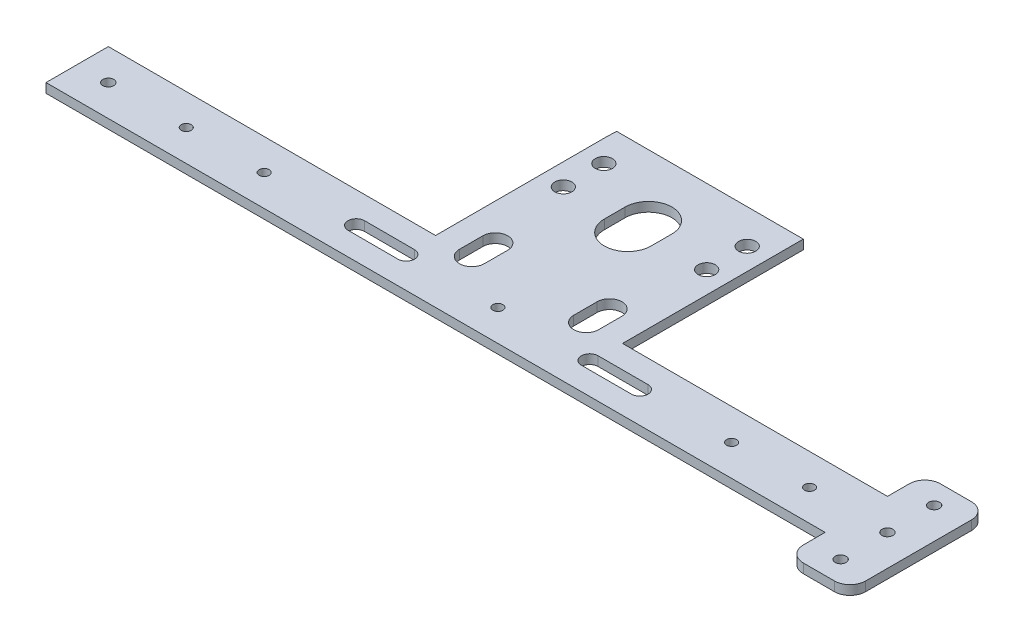
SolidWorks part; units mm, degrees
material "A-玻璃纤维"
ref_plane "前视基准面" through (0, 0, 0) normal (0, 0, 1) x (1, 0, 0)
ref_plane "上视基准面" through (0, 0, 0) normal (0, 1, 0) x (1, 0, 0)
ref_plane "右视基准面" through (0, 0, 0) normal (1, 0, 0) x (0, 0, -1)
sketch "草图1" plane through (0, 0, 0) normal (0, 1, 0) x (1, 0, 0)
  line L1 (-135, 50) -> (135, 50)
  line L2 (-135, 50) -> (-135, -50)
  line L3 (-135, -50) -> (135, -50)
  line L4 (135, 50) -> (135, -50)
  line L5 (-135, 50) -> (135, -50) construction
  line L6 (-135, -50) -> (135, 50) construction
  point P0 (0, 0)
  dimension "D1" = 270
  dimension "D2" = 100
extrude "凸台-拉伸1" add sketch "草图1" along normal blind 3
sketch "草图2" plane through (0, 3, 0) normal (0, 1, 0) x (1, 0, 0)
  line L0 (0, 50) -> (0, -50) construction
  line L1 (135, 50) -> (-135, 50) construction
  line L2 (-135, -50) -> (135, -50) construction
  line L3 (-135, 0) -> (135, 0) construction
  line L4 (-135, 50) -> (-135, -50) construction
  line L5 (135, -50) -> (135, 50) construction
  line L6 (141.2853, -40) -> (-157.6953, -40) construction
  circle A2 centre (-125, 40) radius 1.6
  circle A3 centre (-125, 0) radius 1.6
  circle A4 centre (125, 0) radius 1.6
  circle A5 centre (125, 40) radius 1.6
  circle A6 centre (-125, -40) radius 1.75
  circle A7 centre (-100, -40) radius 1.6
  circle A8 centre (-75, -40) radius 1.6
  circle A9 centre (0, -40) radius 1.6
  circle A10 centre (75, -40) radius 1.6
  circle A11 centre (100, -40) radius 1.6
  circle A12 centre (125, -40) radius 1.75
  dimension "D1" = 3.2
  dimension "D2" = 3.5
  dimension "D3" = 3.2
  dimension "D5" = 10
  dimension "D7" = 25
  dimension "D8" = 50
  dimension "D9" = 40
  dimension "D10" = 40
  dimension "D6" = 10
extrude "切除-拉伸1" cut sketch "草图2" against normal blind 3
sketch "草图4" plane through (0, 3, 0) normal (0, 1, 0) x (1, 0, 0)
  line L0 (0, -106.0486) -> (0, 112.9076) construction
  line L1 (110, -50) -> (110, 50) construction
  line L2 (-135, -50) -> (135, -50) construction
  line L3 (135, 50) -> (-135, 50) construction
  line L4 (91.6667, -50) -> (91.6667, 65) construction
  line L5 (110, -30) -> (110, -23.3333) construction
  line L6 (102.5, -30) -> (102.5, -23.3333)
  line L7 (117.5, -30) -> (117.5, -23.3333)
  line L8 (110, 1.6667) -> (110, 8.3333) construction
  line L9 (102.5, 1.6667) -> (102.5, 8.3333)
  line L10 (117.5, 1.6667) -> (117.5, 8.3333)
  line L11 (110, 28.3333) -> (110, 35) construction
  line L12 (102.5, 28.3333) -> (102.5, 35)
  line L13 (117.5, 28.3333) -> (117.5, 35)
  line L14 (135, -30) -> (-135, -30) construction
  line L15 (135, -50) -> (135, 50) construction
  line L16 (-135, 50) -> (-135, -50) construction
  line L17 (91.6667, -30) -> (91.6667, -22.5) construction
  line L18 (87.6667, -30) -> (87.6667, -22.5)
  line L19 (95.6667, -30) -> (95.6667, -22.5)
  line L20 (91.6667, -10.5) -> (91.6667, -6.5) construction
  line L21 (87.6667, -10.5) -> (87.6667, -6.5)
  line L22 (95.6667, -10.5) -> (95.6667, -6.5)
  line L23 (91.6667, 8.5) -> (91.6667, 12.5) construction
  line L24 (87.6667, 8.5) -> (87.6667, 12.5)
  line L25 (95.6667, 8.5) -> (95.6667, 12.5)
  line L26 (136.9036, 35) -> (-135, 35) construction
  line L27 (91.6667, 35) -> (91.6667, 27.5) construction
  line L28 (95.6667, 35) -> (95.6667, 27.5)
  line L29 (87.6667, 35) -> (87.6667, 27.5)
  line L30 (73.3333, -30) -> (73.3333, -23.3333) construction
  line L31 (65.8333, -30) -> (65.8333, -23.3333) construction
  line L32 (80.8333, -30) -> (80.8333, -23.3333) construction
  line L33 (73.3333, 1.6667) -> (73.3333, 8.3333) construction
  line L34 (65.8333, 1.6667) -> (65.8333, 8.3333)
  line L35 (80.8333, 1.6667) -> (80.8333, 8.3333)
  line L36 (73.3333, 28.3333) -> (73.3333, 35) construction
  line L37 (65.8333, 28.3333) -> (65.8333, 35)
  line L38 (80.8333, 28.3333) -> (80.8333, 35)
  line L39 (55, -30) -> (55, -22.5) construction
  line L40 (51, -30) -> (51, -22.5)
  line L41 (59, -30) -> (59, -22.5)
  line L42 (55, -10.5) -> (55, -6.5) construction
  line L43 (51, -10.5) -> (51, -6.5)
  line L44 (59, -10.5) -> (59, -6.5)
  line L45 (55, 8.5) -> (55, 12.5) construction
  line L46 (51, 8.5) -> (51, 12.5)
  line L47 (59, 8.5) -> (59, 12.5)
  line L48 (55, 35) -> (55, 27.5) construction
  line L49 (59, 35) -> (59, 27.5)
  line L50 (51, 35) -> (51, 27.5)
  line L51 (36.6667, -30) -> (36.6667, -23.3333) construction
  line L52 (29.1667, -30) -> (29.1667, -23.3333)
  line L53 (44.1667, -30) -> (44.1667, -23.3333)
  line L54 (36.6667, 1.6667) -> (36.6667, 8.3333) construction
  line L55 (29.1667, 1.6667) -> (29.1667, 8.3333)
  line L56 (44.1667, 1.6667) -> (44.1667, 8.3333)
  line L57 (36.6667, 28.3333) -> (36.6667, 35) construction
  line L58 (29.1667, 28.3333) -> (29.1667, 35)
  line L59 (44.1667, 28.3333) -> (44.1667, 35)
  line L60 (18.3333, -30) -> (18.3333, -22.5) construction
  line L61 (14.3333, -30) -> (14.3333, -22.5)
  line L62 (22.3333, -30) -> (22.3333, -22.5)
  line L63 (18.3333, -10.5) -> (18.3333, -6.5) construction
  line L64 (14.3333, -10.5) -> (14.3333, -6.5) construction
  line L65 (22.3333, -10.5) -> (22.3333, -6.5) construction
  line L66 (18.3333, 8.5) -> (18.3333, 12.5) construction
  line L67 (14.3333, 8.5) -> (14.3333, 12.5) construction
  line L68 (22.3333, 8.5) -> (22.3333, 12.5) construction
  line L69 (18.3333, 35) -> (18.3333, 27.5) construction
  line L70 (22.3333, 35) -> (22.3333, 27.5)
  line L71 (14.3333, 35) -> (14.3333, 27.5)
  line L72 (0, -30) -> (0, -23.3333) construction
  line L73 (-7.5, -30) -> (-7.5, -23.3333) construction
  line L74 (7.5, -30) -> (7.5, -23.3333) construction
  line L75 (0, 1.6667) -> (0, 8.3333) construction
  line L76 (-7.5, 1.6667) -> (-7.5, 8.3333)
  line L77 (7.5, 1.6667) -> (7.5, 8.3333)
  line L78 (0, 28.3333) -> (0, 35) construction
  line L79 (-7.5, 28.3333) -> (-7.5, 35)
  line L80 (7.5, 28.3333) -> (7.5, 35)
  line L81 (-18.3333, -30) -> (-18.3333, -22.5) construction
  line L82 (-22.3333, -30) -> (-22.3333, -22.5)
  line L83 (-14.3333, -30) -> (-14.3333, -22.5)
  line L84 (-18.3333, -10.5) -> (-18.3333, -6.5) construction
  line L85 (-22.3333, -10.5) -> (-22.3333, -6.5) construction
  line L86 (-14.3333, -10.5) -> (-14.3333, -6.5) construction
  line L87 (-18.3333, 8.5) -> (-18.3333, 12.5) construction
  line L88 (-22.3333, 8.5) -> (-22.3333, 12.5) construction
  line L89 (-14.3333, 8.5) -> (-14.3333, 12.5) construction
  line L90 (-18.3333, 35) -> (-18.3333, 27.5) construction
  line L91 (-14.3333, 35) -> (-14.3333, 27.5)
  line L92 (-22.3333, 35) -> (-22.3333, 27.5)
  line L93 (-36.6667, -30) -> (-36.6667, -23.3333) construction
  line L94 (-44.1667, -30) -> (-44.1667, -23.3333)
  line L95 (-29.1667, -30) -> (-29.1667, -23.3333)
  line L96 (-36.6667, 1.6667) -> (-36.6667, 8.3333) construction
  line L97 (-44.1667, 1.6667) -> (-44.1667, 8.3333)
  line L98 (-29.1667, 1.6667) -> (-29.1667, 8.3333)
  line L99 (-36.6667, 28.3333) -> (-36.6667, 35) construction
  line L100 (-44.1667, 28.3333) -> (-44.1667, 35)
  line L101 (-29.1667, 28.3333) -> (-29.1667, 35)
  line L102 (-55, -30) -> (-55, -22.5) construction
  line L103 (-59, -30) -> (-59, -22.5)
  line L104 (-51, -30) -> (-51, -22.5)
  line L105 (-55, -10.5) -> (-55, -6.5) construction
  line L106 (-59, -10.5) -> (-59, -6.5)
  line L107 (-51, -10.5) -> (-51, -6.5)
  line L108 (-55, 8.5) -> (-55, 12.5) construction
  line L109 (-59, 8.5) -> (-59, 12.5)
  line L110 (-51, 8.5) -> (-51, 12.5)
  line L111 (-55, 35) -> (-55, 27.5) construction
  line L112 (-51, 35) -> (-51, 27.5)
  line L113 (-59, 35) -> (-59, 27.5)
  line L114 (-73.3333, -30) -> (-73.3333, -23.3333) construction
  line L115 (-80.8333, -30) -> (-80.8333, -23.3333) construction
  line L116 (-65.8333, -30) -> (-65.8333, -23.3333) construction
  line L117 (-73.3333, 1.6667) -> (-73.3333, 8.3333) construction
  line L118 (-80.8333, 1.6667) -> (-80.8333, 8.3333)
  line L119 (-65.8333, 1.6667) -> (-65.8333, 8.3333)
  line L120 (-73.3333, 28.3333) -> (-73.3333, 35) construction
  line L121 (-80.8333, 28.3333) -> (-80.8333, 35)
  line L122 (-65.8333, 28.3333) -> (-65.8333, 35)
  line L123 (-91.6667, -30) -> (-91.6667, -22.5) construction
  line L124 (-95.6667, -30) -> (-95.6667, -22.5)
  line L125 (-87.6667, -30) -> (-87.6667, -22.5)
  line L126 (-91.6667, -10.5) -> (-91.6667, -6.5) construction
  line L127 (-95.6667, -10.5) -> (-95.6667, -6.5)
  line L128 (-87.6667, -10.5) -> (-87.6667, -6.5)
  line L129 (-91.6667, 8.5) -> (-91.6667, 12.5) construction
  line L130 (-95.6667, 8.5) -> (-95.6667, 12.5)
  line L131 (-87.6667, 8.5) -> (-87.6667, 12.5)
  line L132 (-91.6667, 35) -> (-91.6667, 27.5) construction
  line L133 (-87.6667, 35) -> (-87.6667, 27.5)
  line L134 (-95.6667, 35) -> (-95.6667, 27.5)
  line L135 (-110, -30) -> (-110, -23.3333) construction
  line L136 (-102.5, -30) -> (-102.5, -23.3333)
  line L137 (-117.5, -30) -> (-117.5, -23.3333)
  line L138 (-110, 1.6667) -> (-110, 8.3333) construction
  line L139 (-102.5, 1.6667) -> (-102.5, 8.3333)
  line L140 (-117.5, 1.6667) -> (-117.5, 8.3333)
  line L141 (-110, 28.3333) -> (-110, 35) construction
  line L142 (-102.5, 28.3333) -> (-102.5, 35)
  line L143 (-117.5, 28.3333) -> (-117.5, 35)
  line L144 (110, 35) -> (91.6667, 35) construction
  line L145 (91.6667, 35) -> (73.3333, 35) construction
  line L146 (110, 35) -> (91.6667, 35) construction
  line L147 (91.6667, 35) -> (73.3333, 35) construction
  line L148 (135, 50) -> (-135, 50) construction
  arc A0 (102.5, -30) -> (117.5, -30) centre (110, -30) ccw
  arc A1 (117.5, -23.3333) -> (102.5, -23.3333) centre (110, -23.3333) ccw
  arc A2 (102.5, 1.6667) -> (117.5, 1.6667) centre (110, 1.6667) ccw
  arc A3 (117.5, 8.3333) -> (102.5, 8.3333) centre (110, 8.3333) ccw
  arc A4 (102.5, 28.3333) -> (117.5, 28.3333) centre (110, 28.3333) ccw
  arc A5 (117.5, 35) -> (102.5, 35) centre (110, 35) ccw
  arc A6 (87.6667, -30) -> (95.6667, -30) centre (91.6667, -30) ccw
  arc A7 (95.6667, -22.5) -> (87.6667, -22.5) centre (91.6667, -22.5) ccw
  arc A8 (87.6667, -10.5) -> (95.6667, -10.5) centre (91.6667, -10.5) ccw
  arc A9 (95.6667, -6.5) -> (87.6667, -6.5) centre (91.6667, -6.5) ccw
  arc A10 (87.6667, 8.5) -> (95.6667, 8.5) centre (91.6667, 8.5) ccw
  arc A11 (95.6667, 12.5) -> (87.6667, 12.5) centre (91.6667, 12.5) ccw
  arc A12 (95.6667, 35) -> (87.6667, 35) centre (91.6667, 35) ccw
  arc A13 (87.6667, 27.5) -> (95.6667, 27.5) centre (91.6667, 27.5) ccw
  arc A14 (65.8333, -30) -> (80.8333, -30) centre (73.3333, -30) ccw construction
  arc A15 (80.8333, -23.3333) -> (65.8333, -23.3333) centre (73.3333, -23.3333) ccw construction
  arc A16 (65.8333, 1.6667) -> (80.8333, 1.6667) centre (73.3333, 1.6667) ccw
  arc A17 (80.8333, 8.3333) -> (65.8333, 8.3333) centre (73.3333, 8.3333) ccw
  arc A18 (65.8333, 28.3333) -> (80.8333, 28.3333) centre (73.3333, 28.3333) ccw
  arc A19 (80.8333, 35) -> (65.8333, 35) centre (73.3333, 35) ccw
  arc A20 (51, -30) -> (59, -30) centre (55, -30) ccw
  arc A21 (59, -22.5) -> (51, -22.5) centre (55, -22.5) ccw
  arc A22 (51, -10.5) -> (59, -10.5) centre (55, -10.5) ccw
  arc A23 (59, -6.5) -> (51, -6.5) centre (55, -6.5) ccw
  arc A24 (51, 8.5) -> (59, 8.5) centre (55, 8.5) ccw
  arc A25 (59, 12.5) -> (51, 12.5) centre (55, 12.5) ccw
  arc A26 (59, 35) -> (51, 35) centre (55, 35) ccw
  arc A27 (51, 27.5) -> (59, 27.5) centre (55, 27.5) ccw
  arc A28 (29.1667, -30) -> (44.1667, -30) centre (36.6667, -30) ccw
  arc A29 (44.1667, -23.3333) -> (29.1667, -23.3333) centre (36.6667, -23.3333) ccw
  arc A30 (29.1667, 1.6667) -> (44.1667, 1.6667) centre (36.6667, 1.6667) ccw
  arc A31 (44.1667, 8.3333) -> (29.1667, 8.3333) centre (36.6667, 8.3333) ccw
  arc A32 (29.1667, 28.3333) -> (44.1667, 28.3333) centre (36.6667, 28.3333) ccw
  arc A33 (44.1667, 35) -> (29.1667, 35) centre (36.6667, 35) ccw
  arc A34 (14.3333, -30) -> (22.3333, -30) centre (18.3333, -30) ccw
  arc A35 (22.3333, -22.5) -> (14.3333, -22.5) centre (18.3333, -22.5) ccw
  arc A36 (14.3333, -10.5) -> (22.3333, -10.5) centre (18.3333, -10.5) ccw construction
  arc A37 (22.3333, -6.5) -> (14.3333, -6.5) centre (18.3333, -6.5) ccw construction
  arc A38 (14.3333, 8.5) -> (22.3333, 8.5) centre (18.3333, 8.5) ccw construction
  arc A39 (22.3333, 12.5) -> (14.3333, 12.5) centre (18.3333, 12.5) ccw construction
  arc A40 (22.3333, 35) -> (14.3333, 35) centre (18.3333, 35) ccw
  arc A41 (14.3333, 27.5) -> (22.3333, 27.5) centre (18.3333, 27.5) ccw
  arc A42 (-7.5, -30) -> (7.5, -30) centre (0, -30) ccw construction
  arc A43 (7.5, -23.3333) -> (-7.5, -23.3333) centre (0, -23.3333) ccw construction
  arc A44 (-7.5, 1.6667) -> (7.5, 1.6667) centre (0, 1.6667) ccw
  arc A45 (7.5, 8.3333) -> (-7.5, 8.3333) centre (0, 8.3333) ccw
  arc A46 (-7.5, 28.3333) -> (7.5, 28.3333) centre (0, 28.3333) ccw
  arc A47 (7.5, 35) -> (-7.5, 35) centre (0, 35) ccw
  arc A48 (-22.3333, -30) -> (-14.3333, -30) centre (-18.3333, -30) ccw
  arc A49 (-14.3333, -22.5) -> (-22.3333, -22.5) centre (-18.3333, -22.5) ccw
  arc A50 (-22.3333, -10.5) -> (-14.3333, -10.5) centre (-18.3333, -10.5) ccw construction
  arc A51 (-14.3333, -6.5) -> (-22.3333, -6.5) centre (-18.3333, -6.5) ccw construction
  arc A52 (-22.3333, 8.5) -> (-14.3333, 8.5) centre (-18.3333, 8.5) ccw construction
  arc A53 (-14.3333, 12.5) -> (-22.3333, 12.5) centre (-18.3333, 12.5) ccw construction
  arc A54 (-14.3333, 35) -> (-22.3333, 35) centre (-18.3333, 35) ccw
  arc A55 (-22.3333, 27.5) -> (-14.3333, 27.5) centre (-18.3333, 27.5) ccw
  arc A56 (-44.1667, -30) -> (-29.1667, -30) centre (-36.6667, -30) ccw
  arc A57 (-29.1667, -23.3333) -> (-44.1667, -23.3333) centre (-36.6667, -23.3333) ccw
  arc A58 (-44.1667, 1.6667) -> (-29.1667, 1.6667) centre (-36.6667, 1.6667) ccw
  arc A59 (-29.1667, 8.3333) -> (-44.1667, 8.3333) centre (-36.6667, 8.3333) ccw
  arc A60 (-44.1667, 28.3333) -> (-29.1667, 28.3333) centre (-36.6667, 28.3333) ccw
  arc A61 (-29.1667, 35) -> (-44.1667, 35) centre (-36.6667, 35) ccw
  arc A62 (-59, -30) -> (-51, -30) centre (-55, -30) ccw
  arc A63 (-51, -22.5) -> (-59, -22.5) centre (-55, -22.5) ccw
  arc A64 (-59, -10.5) -> (-51, -10.5) centre (-55, -10.5) ccw
  arc A65 (-51, -6.5) -> (-59, -6.5) centre (-55, -6.5) ccw
  arc A66 (-59, 8.5) -> (-51, 8.5) centre (-55, 8.5) ccw
  arc A67 (-51, 12.5) -> (-59, 12.5) centre (-55, 12.5) ccw
  arc A68 (-51, 35) -> (-59, 35) centre (-55, 35) ccw
  arc A69 (-59, 27.5) -> (-51, 27.5) centre (-55, 27.5) ccw
  arc A70 (-80.8333, -30) -> (-65.8333, -30) centre (-73.3333, -30) ccw construction
  arc A71 (-65.8333, -23.3333) -> (-80.8333, -23.3333) centre (-73.3333, -23.3333) ccw construction
  arc A72 (-80.8333, 1.6667) -> (-65.8333, 1.6667) centre (-73.3333, 1.6667) ccw
  arc A73 (-65.8333, 8.3333) -> (-80.8333, 8.3333) centre (-73.3333, 8.3333) ccw
  arc A74 (-80.8333, 28.3333) -> (-65.8333, 28.3333) centre (-73.3333, 28.3333) ccw
  arc A75 (-65.8333, 35) -> (-80.8333, 35) centre (-73.3333, 35) ccw
  arc A76 (-95.6667, -30) -> (-87.6667, -30) centre (-91.6667, -30) ccw
  arc A77 (-87.6667, -22.5) -> (-95.6667, -22.5) centre (-91.6667, -22.5) ccw
  arc A78 (-95.6667, -10.5) -> (-87.6667, -10.5) centre (-91.6667, -10.5) ccw
  arc A79 (-87.6667, -6.5) -> (-95.6667, -6.5) centre (-91.6667, -6.5) ccw
  arc A80 (-95.6667, 8.5) -> (-87.6667, 8.5) centre (-91.6667, 8.5) ccw
  arc A81 (-87.6667, 12.5) -> (-95.6667, 12.5) centre (-91.6667, 12.5) ccw
  arc A82 (-87.6667, 35) -> (-95.6667, 35) centre (-91.6667, 35) ccw
  arc A83 (-95.6667, 27.5) -> (-87.6667, 27.5) centre (-91.6667, 27.5) ccw
  arc A84 (-102.5, -30) -> (-117.5, -30) centre (-110, -30) cw
  arc A85 (-117.5, -23.3333) -> (-102.5, -23.3333) centre (-110, -23.3333) cw
  arc A86 (-102.5, 1.6667) -> (-117.5, 1.6667) centre (-110, 1.6667) cw
  arc A87 (-117.5, 8.3333) -> (-102.5, 8.3333) centre (-110, 8.3333) cw
  arc A88 (-102.5, 28.3333) -> (-117.5, 28.3333) centre (-110, 28.3333) cw
  arc A89 (-117.5, 35) -> (-102.5, 35) centre (-110, 35) cw
  point P13 (110, -26.6667)
  point P18 (110, 5)
  point P25 (110, 31.6667)
  point P40 (91.6667, -26.25)
  point P45 (91.6667, -8.5)
  point P52 (91.6667, 10.5)
  point P61 (91.6667, 31.25)
  point P72 (73.3333, -26.6667)
  point P77 (73.3333, 5)
  point P84 (73.3333, 31.6667)
  point P93 (55, -26.25)
  point P98 (55, -8.5)
  point P105 (55, 10.5)
  point P112 (55, 31.25)
  point P121 (36.6667, -26.6667)
  point P126 (36.6667, 5)
  point P133 (36.6667, 31.6667)
  point P142 (18.3333, -26.25)
  point P147 (18.3333, -8.5)
  point P154 (18.3333, 10.5)
  point P161 (18.3333, 31.25)
  point P170 (0, -26.6667)
  point P175 (0, 5)
  point P182 (0, 31.6667)
  point P191 (-18.3333, -26.25)
  point P196 (-18.3333, -8.5)
  point P203 (-18.3333, 10.5)
  point P210 (-18.3333, 31.25)
  point P219 (-36.6667, -26.6667)
  point P224 (-36.6667, 5)
  point P231 (-36.6667, 31.6667)
  point P240 (-55, -26.25)
  point P245 (-55, -8.5)
  point P252 (-55, 10.5)
  point P259 (-55, 31.25)
  point P268 (-73.3333, -26.6667)
  point P273 (-73.3333, 5)
  point P280 (-73.3333, 31.6667)
  point P289 (-91.6667, -26.25)
  point P294 (-91.6667, -8.5)
  point P301 (-91.6667, 10.5)
  point P308 (-91.6667, 31.25)
  point P317 (-110, -26.6667)
  point P324 (-110, 5)
  point P331 (-110, 31.6667)
  dimension "D3" = 25
  dimension "D6" = 20
  dimension "D9" = 12
  dimension "D10" = 15
  dimension "D11" = 15
  dimension "D1" = 15
  dimension "D2" = 25
  dimension "D4" = 20
  dimension "D5" = 15
  dimension "D7" = 8
  dimension "D8" = 7.5
  dimension "D13" = 6
extrude "切除-拉伸2" cut sketch "草图4" against normal blind 10
sketch "草图5" plane through (0, 3, 0) normal (0, 1, 0) x (1, 0, 0)
  circle A0 centre (23, 17) radius 2.75 construction
  circle A1 centre (23, 4) radius 2.75 construction
  circle A2 centre (-23, 17) radius 2.75 construction
  circle A3 centre (-23, 4) radius 2.75 construction
  circle A4 centre (23, 17) radius 2.75
  circle A5 centre (23, 4) radius 2.75
  circle A6 centre (-23, 17) radius 2.75
  circle A7 centre (-23, 4) radius 2.75
extrude "切除-拉伸3" cut sketch "草图5" against normal blind 10
sketch "草图6" plane through (0, 0, 0) normal (0, -1, 0) x (1, 0, 0)
  line L0 (0, 0) -> (0, -97.1069) construction
  line L1 (135, -50) -> (-135, -50) construction
  line L2 (-30, -50) -> (-135, -50)
  line L3 (-30, -50) -> (-30, 30)
  line L4 (-30, 30) -> (-135, 30)
  line L5 (-135, -50) -> (-135, 30)
  line L6 (-135, -50) -> (-135, 50) construction
  line L7 (-135, 50) -> (135, 50) construction
  line L8 (135, -50) -> (135, 30)
  line L9 (30, 30) -> (135, 30)
  line L10 (30, -50) -> (30, 30)
  line L11 (30, -50) -> (135, -50)
  line L13 (-30, -50) -> (30, -50)
  line L14 (-30, -50) -> (-30, -28)
  line L15 (-30, -28) -> (30, -28)
  line L16 (30, -50) -> (30, -28)
  dimension "D1" = 20
  dimension "D2" = 30
  dimension "D3" = 22
extrude "切除-拉伸4" cut sketch "草图6" against normal blind 10 contours L5 L2 L3 L4 | L15 L0 L13 L10 | L10 L11 L8 L9 | L0 L15 L3 L13
sketch "草图7" plane through (0, 0, 0) normal (0, -1, 0) x (1, 0, 0)
  line L0 (-59.102, -10.5) -> (77.1983, -10.5)
  line L1 (52.8428, -4) -> (-87.0205, -4)
  circle A0 centre (-23, -17) radius 2.75 construction
  circle A1 centre (-23, -4) radius 2.75 construction
  circle A3 centre (23, -4) radius 2.75 construction
  circle A4 centre (23, -4) radius 2.75
sketch "草图8" plane through (0, 3, 0) normal (0, 1, 0) x (1, 0, 0)
  line L0 (117.5, -30) -> (102.5, -30)
  arc A0 (102.5, -30) -> (117.5, -30) centre (110, -30) ccw
  dimension "D1" = 7.5
extrude "凸台-拉伸2" add sketch "草图8" against normal blind 3
sketch "草图9" plane through (0, 3, 0) normal (0, 1, 0) x (1, 0, 0)
  line L0 (95.6667, -30) -> (87.6667, -30)
  arc A0 (87.6667, -30) -> (95.6667, -30) centre (91.6667, -30) ccw
  dimension "D1" = 4
extrude "凸台-拉伸3" add sketch "草图9" against normal blind 3
sketch "草图10" plane through (0, 3, 0) normal (0, 1, 0) x (1, 0, 0)
  line L0 (59, -30) -> (51, -30)
  arc A0 (51, -30) -> (59, -30) centre (55, -30) ccw
  dimension "D1" = 4
extrude "凸台-拉伸4" add sketch "草图10" against normal blind 3
sketch "草图11" plane through (0, 3, 0) normal (0, 1, 0) x (1, 0, 0)
  line L0 (44.1667, -30) -> (30, -30)
  line L1 (30, -19.8974) -> (30, -30)
  line L2 (30, -19.8974) -> (28.7529, -21.8943)
  line L3 (28.7529, -21.8943) -> (29.1667, -30)
  arc A0 (44.1667, -30) -> (29.1667, -30) centre (36.6667, -30) cw
  dimension "D1" = 7.5
extrude "凸台-拉伸6" add sketch "草图11" against normal blind 3
sketch "草图12" plane through (0, 3, 0) normal (0, 1, 0) x (1, 0, 0)
  line L0 (30, -1.7693) -> (30, 11.7693)
  line L1 (30, 11.7693) -> (29.04, 10.1343)
  line L2 (29.04, 10.1343) -> (28.8099, -1.7693)
  line L3 (28.8099, -1.7693) -> (30, -1.7693)
extrude "凸台-拉伸7" add sketch "草图12" against normal blind 3
sketch "草图13" plane through (0, 3, 0) normal (0, 1, 0) x (1, 0, 0)
  line L0 (29.1741, 28) -> (30, 28)
  line L1 (30, 24.8974) -> (30, 28)
  line L2 (30, 24.8974) -> (29.1741, 24.8974)
  line L3 (29.1741, 24.8974) -> (29.1741, 28)
extrude "凸台-拉伸8" add sketch "草图13" against normal blind 3
sketch "草图14" plane through (0, 3, 0) normal (0, 1, 0) x (1, 0, 0)
  line L0 (22.3333, 28) -> (14.3333, 28)
  line L1 (22.3333, 28) -> (22.3333, 22.8614)
  line L2 (22.3333, 22.8614) -> (14.1712, 22.8614)
  line L3 (14.1712, 22.8614) -> (14.3333, 28)
extrude "凸台-拉伸9" add sketch "草图14" against normal blind 3
sketch "草图15" plane through (0, 3, 0) normal (0, 1, 0) x (1, 0, 0)
  line L0 (7.4926, 28) -> (-7.4926, 28)
  arc A0 (-7.4926, 28) -> (7.4926, 28) centre (0, 28) ccw
  dimension "D1" = 7.4926
extrude "凸台-拉伸10" add sketch "草图15" against normal blind 3
sketch "草图16" plane through (0, 3, 0) normal (0, 1, 0) x (1, 0, 0)
  line L0 (-14.3333, 28) -> (-22.3333, 28)
  line L1 (-14.3333, 28) -> (-14.3333, 22.5669)
  line L2 (-14.3333, 22.5669) -> (-22.3333, 22.5669)
  line L3 (-22.3333, 22.5669) -> (-22.3333, 28)
extrude "凸台-拉伸11" add sketch "草图16" against normal blind 3
sketch "草图17" plane through (0, 3, 0) normal (0, 1, 0) x (1, 0, 0)
  line L0 (-29.1741, 28) -> (-29.8904, 28)
  line L1 (-30, 24.8974) -> (-29.8904, 28)
  line L2 (-30, 24.8974) -> (-29.1741, 24.8974)
  line L3 (-29.1741, 24.8974) -> (-29.1741, 28)
extrude "凸台-拉伸12" add sketch "草图17" against normal blind 3
sketch "草图18" plane through (0, 3, 0) normal (0, 1, 0) x (1, 0, 0)
  line L0 (-30, -1.7693) -> (-30, 11.7693)
  line L1 (-30, 11.7693) -> (-30, 24.8974) construction
  line L2 (-30, 11.7693) -> (-28.8974, 11.7693)
  line L3 (-28.8974, 11.7693) -> (-28.8974, -1.7693)
  line L4 (-28.8974, -1.7693) -> (-30, -1.7693)
  arc A0 (-29.1667, 8.3333) -> (-30, 11.7693) centre (-36.6667, 8.3333) ccw construction
extrude "凸台-拉伸13" add sketch "草图18" against normal blind 3
sketch "草图19" plane through (0, 3, 0) normal (0, 1, 0) x (1, 0, 0)
  line L0 (-44.1667, -30) -> (-30, -30)
  line L1 (-30, -19.8974) -> (-30, -30)
  line L2 (-29.1667, -30) -> (-29.1667, -19.8974)
  line L3 (-29.1667, -19.8974) -> (-30, -19.8974)
  arc A0 (-44.1667, -30) -> (-29.1667, -30) centre (-36.6667, -30) ccw construction
  arc A1 (-44.1667, -30) -> (-29.1667, -30) centre (-36.6667, -30) ccw
  dimension "D1" = 7.5
extrude "凸台-拉伸14" add sketch "草图19" against normal blind 3
sketch "草图20" plane through (0, 3, 0) normal (0, 1, 0) x (1, 0, 0)
  line L0 (-51, -30) -> (-59, -30)
  arc A0 (-59, -30) -> (-51, -30) centre (-55, -30) ccw
  dimension "D1" = 4
extrude "凸台-拉伸15" add sketch "草图20" against normal blind 3
sketch "草图21" plane through (0, 3, 0) normal (0, 1, 0) x (1, 0, 0)
  line L0 (-87.6667, -30) -> (-95.6667, -30)
  arc A0 (-95.6667, -30) -> (-87.6667, -30) centre (-91.6667, -30) ccw construction
  arc A1 (-95.6667, -30) -> (-87.6667, -30) centre (-91.6667, -30) ccw
  dimension "D1" = 4
extrude "凸台-拉伸16" add sketch "草图21" against normal blind 3
sketch "草图22" plane through (0, 3, 0) normal (0, 1, 0) x (1, 0, 0)
  line L0 (-102.5, -30) -> (-117.5, -30)
  arc A0 (-117.5, -30) -> (-102.5, -30) centre (-110, -30) ccw
  dimension "D1" = 7.5
extrude "凸台-拉伸17" add sketch "草图22" against normal blind 3
sketch "草图23" plane through (0, 3, 0) normal (0, 1, 0) x (1, 0, 0)
  line L0 (75, -40) -> (0, -40) construction
  line L1 (0.0548, 28) -> (0, -50) construction
  line L2 (30, 28) -> (-29.8904, 28) construction
  line L3 (-135, -50) -> (135, -50) construction
  line L4 (37.5, -40) -> (37.5, -50) construction
  line L5 (45.5227, -40) -> (29.4773, -40) construction
  line L6 (45.5227, -42.6584) -> (29.4773, -42.6584)
  line L7 (45.5227, -37.3416) -> (29.4773, -37.3416)
  line L8 (-45.5086, -39.936) -> (-29.4632, -39.9586) construction
  line L9 (-45.5123, -42.5945) -> (-29.467, -42.617)
  line L10 (-45.5048, -37.2776) -> (-29.4595, -37.3002)
  arc A0 (45.5227, -42.6584) -> (45.5227, -37.3416) centre (45.5227, -40) ccw
  arc A1 (29.4773, -37.3416) -> (29.4773, -42.6584) centre (29.4773, -40) ccw
  arc A2 (-45.5123, -42.5945) -> (-45.5048, -37.2776) centre (-45.5086, -39.936) cw
  arc A3 (-29.4595, -37.3002) -> (-29.467, -42.617) centre (-29.4632, -39.9586) cw
  point P14 (37.5, -40)
  point P21 (-37.4859, -39.9473)
extrude "切除-拉伸5" cut sketch "草图23" against normal blind 3
sketch "草图24" plane through (0, 0, 0) normal (0, -1, 0) x (1, 0, 0)
  line L0 (135, 50) -> (135, 62)
  line L1 (135, 62) -> (115, 62)
  line L2 (115, 62) -> (115, 50)
  line L3 (-135, 50) -> (135, 50) construction
  line L4 (115, 50) -> (135, 50)
extrude "凸台-拉伸18" add sketch "草图24" against normal up to surface (3 mm away) up to face at (37.5, 3, 40)
sketch "草图25" plane through (0, 0, 0) normal (0, -1, 0) x (1, 0, 0)
  line L0 (135, 30) -> (135, 18)
  line L1 (135, 18) -> (115, 18)
  line L2 (115, 18) -> (115, 30)
  line L3 (30, 30) -> (135, 30) construction
  line L4 (115, 30) -> (135, 30)
extrude "凸台-拉伸19" add sketch "草图25" against normal up to surface (3 mm away) up to face at (37.5, 3, 40)
sketch "草图26" plane through (0, 3, 0) normal (0, 1, 0) x (1, 0, 0)
  line L0 (125, -40) -> (125, -55) construction
  line L1 (125, -40) -> (125, -25) construction
  circle A0 centre (125, -55) radius 1.75
  circle A1 centre (125, -25) radius 1.75
extrude "切除-拉伸6" cut sketch "草图26" against normal through all
fillet "圆角1" radius 5 4 edges at (135, 1.5, 18) (115, 1.5, 18) (135, 1.5, 62) (115, 1.5, 62)
